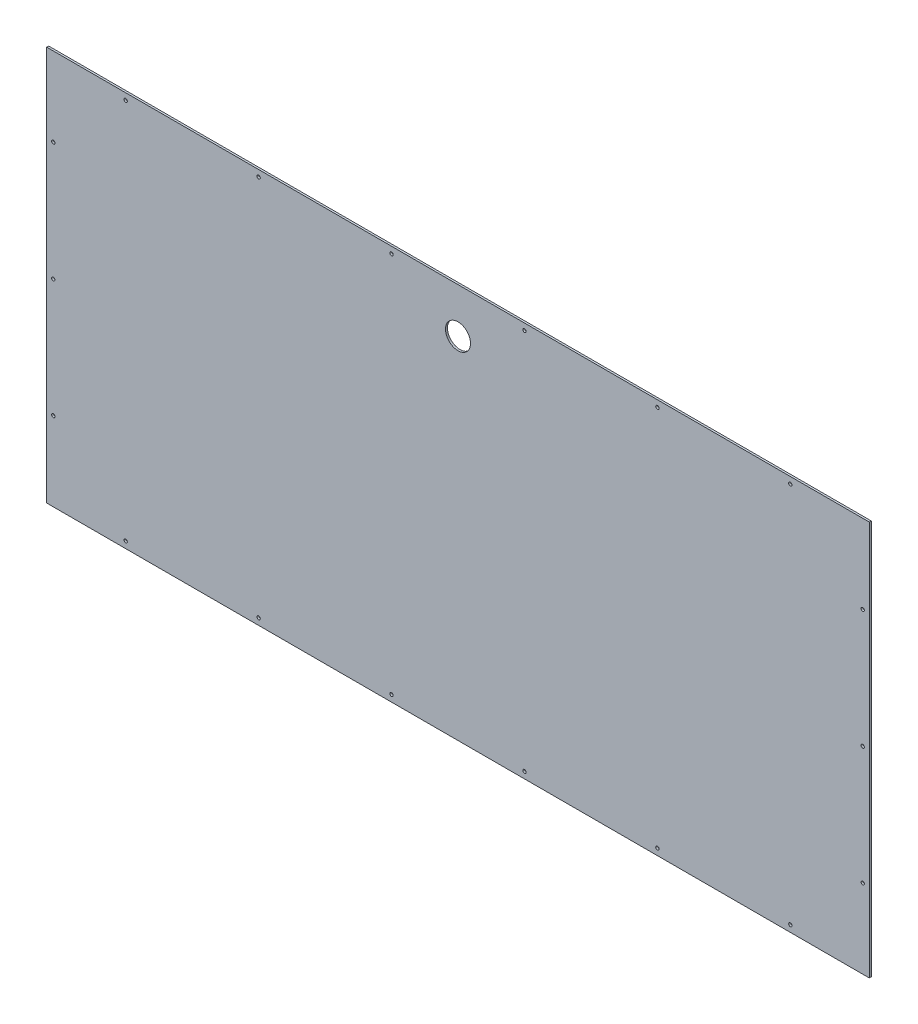
SolidWorks part; units mm, degrees
ref_plane "Front Plane" through (0, 0, 0) normal (0, 0, 1) x (1, 0, 0)
ref_plane "Top Plane" through (0, 0, 0) normal (0, 1, 0) x (1, 0, 0)
ref_plane "Right Plane" through (0, 0, 0) normal (1, 0, 0) x (0, 0, -1)
sketch "Sketch1" plane through (0, 0, 0) normal (0, 0, 1) x (1, 0, 0)
  line L1 (-625, 300) -> (625, 300)
  line L2 (-625, 300) -> (-625, -300)
  line L3 (-625, -300) -> (625, -300)
  line L4 (625, 300) -> (625, -300)
  line L5 (-625, 300) -> (625, -300) construction
  line L6 (-625, -300) -> (625, 300) construction
  circle A0 centre (303, 290) radius 2.55
  circle A1 centre (101, 290) radius 2.55
  circle A2 centre (-101, 290) radius 2.55
  circle A3 centre (-303, 290) radius 2.55
  circle A4 centre (505, 290) radius 2.55
  circle A5 centre (505, -290) radius 2.55
  circle A6 centre (-505, 290) radius 2.55
  circle A7 centre (303, -290) radius 2.55
  circle A8 centre (101, -290) radius 2.55
  circle A9 centre (-101, -290) radius 2.55
  circle A10 centre (615, 180) radius 2.55
  circle A11 centre (-615, 180) radius 2.55
  circle A12 centre (-615, 0) radius 2.55
  circle A13 centre (-615, -180) radius 2.55
  circle A14 centre (-303, -290) radius 2.55
  circle A15 centre (615, 0) radius 2.55
  circle A16 centre (615, -180) radius 2.55
  circle A17 centre (-505, -290) radius 2.55
  circle A18 centre (0, 232) radius 19
  point P0 (0, 0)
  dimension "D3" = 120
  dimension "D4" = 10
  dimension "D6" = 120
  dimension "D7" = 10
  dimension "D8" = 10
  dimension "D9" = 120
  dimension "D10" = 10
  dimension "D11" = 5.1
  dimension "D12" = 120
  dimension "D14" = 3
  dimension "D16" = 120
  dimension "D17" = 180
  dimension "D18" = 120
  dimension "D20" = 120
  dimension "D21" = 38
  dimension "D23" = 625
  dimension "D1" = 600
  dimension "D2" = 1250
  dimension "D15" = 120
  dimension "D22" = 68
  dimension "D13" = 3
  dimension "D5" = 6
  dimension "D19" = 6
extrude "Boss-Extrude1" add sketch "Sketch1" along normal blind 3
